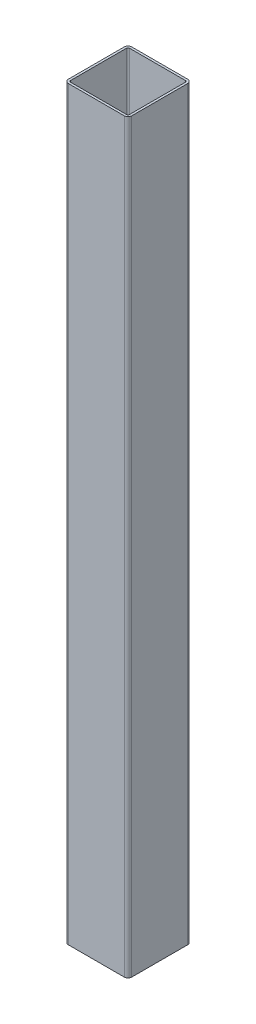
SolidWorks part; units mm, degrees
ref_plane "Спереди" through (0, 0, 0) normal (0, 0, 1) x (1, 0, 0)
ref_plane "Сверху" through (0, 0, 0) normal (0, 1, 0) x (1, 0, 0)
ref_plane "Справа" through (0, 0, 0) normal (1, 0, 0) x (0, 0, -1)
sketch "Эскиз1" plane through (0, 0, 0) normal (0, 1, 0) x (1, 0, 0)
  line L1 (-37.5, 42.5) -> (37.5, 42.5)
  line L2 (-42.5, 37.5) -> (-42.5, -37.5)
  line L3 (-37.5, -42.5) -> (37.5, -42.5)
  line L4 (42.5, 37.5) -> (42.5, -37.5)
  line L5 (-42.5, 42.5) -> (42.5, -42.5) construction
  line L6 (-42.5, -42.5) -> (42.5, 42.5) construction
  arc A0 (37.5, -42.5) -> (42.5, -37.5) centre (37.5, -37.5) ccw
  arc A1 (37.5, 42.5) -> (42.5, 37.5) centre (37.5, 37.5) cw
  arc A2 (-37.5, 42.5) -> (-42.5, 37.5) centre (-37.5, 37.5) ccw
  arc A3 (-42.5, -37.5) -> (-37.5, -42.5) centre (-37.5, -37.5) ccw
  point P0 (0, 0)
  dimension "D3" = 5
  dimension "D1" = 85
  dimension "D2" = 85
extrude "Вытянуть-Тонкостенный1" add sketch "Эскиз1" along normal blind 1000 thin
